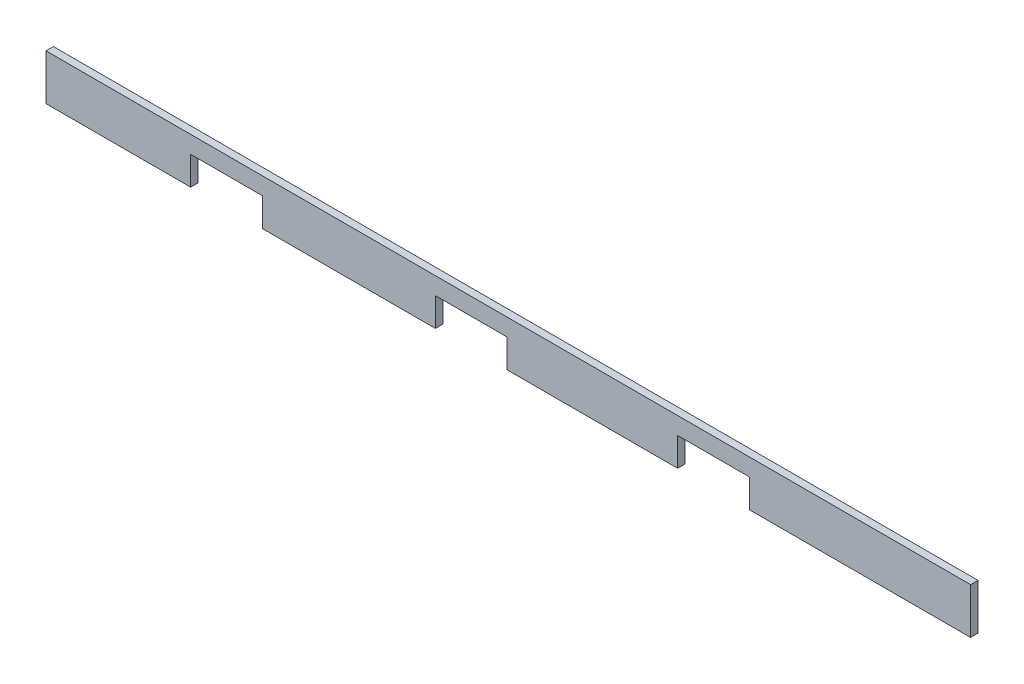
SolidWorks part; units mm, degrees
ref_plane "Front Plane" through (0, 0, 0) normal (0, 0, 1) x (1, 0, 0)
ref_plane "Top Plane" through (0, 0, 0) normal (0, 1, 0) x (1, 0, 0)
ref_plane "Right Plane" through (0, 0, 0) normal (1, 0, 0) x (0, 0, -1)
sketch "Sketch1" plane through (0, 0, 0) normal (0, 0, 1) x (1, 0, 0)
  line L1 (0, 234.95) -> (4749.8, 234.95)
  line L2 (0, 234.95) -> (0, 0)
  line L3 (0, 0) -> (4749.8, 0)
  line L4 (4749.8, 234.95) -> (4749.8, 0)
  line L5 (742.95, 0) -> (1111.25, 0)
  line L6 (742.95, 0) -> (742.95, 146.05)
  line L7 (742.95, 146.05) -> (1111.25, 146.05)
  line L8 (1111.25, 0) -> (1111.25, 146.05)
  line L9 (2000.25, 0) -> (2368.55, 0)
  line L10 (2000.25, 0) -> (2000.25, 146.05)
  line L11 (2000.25, 146.05) -> (2368.55, 146.05)
  line L12 (2368.55, 0) -> (2368.55, 146.05)
  line L13 (3244.85, 0) -> (3613.15, 0)
  line L14 (3244.85, 0) -> (3244.85, 146.05)
  line L15 (3244.85, 146.05) -> (3613.15, 146.05)
  line L16 (3613.15, 0) -> (3613.15, 146.05)
  dimension "D1" = 234.95
  dimension "D2" = 4749.8
  dimension "D3" = 88.9
  dimension "D4" = 742.95
  dimension "D5" = 368.3
  dimension "D6" = 1136.65
  dimension "D7" = 876.3
extrude "Boss-Extrude1" add sketch "Sketch1" along normal blind 38.1 contours L16 L3 L4 L1 L2 L6 L7 L8 L10 L11 L12 L14 L15
